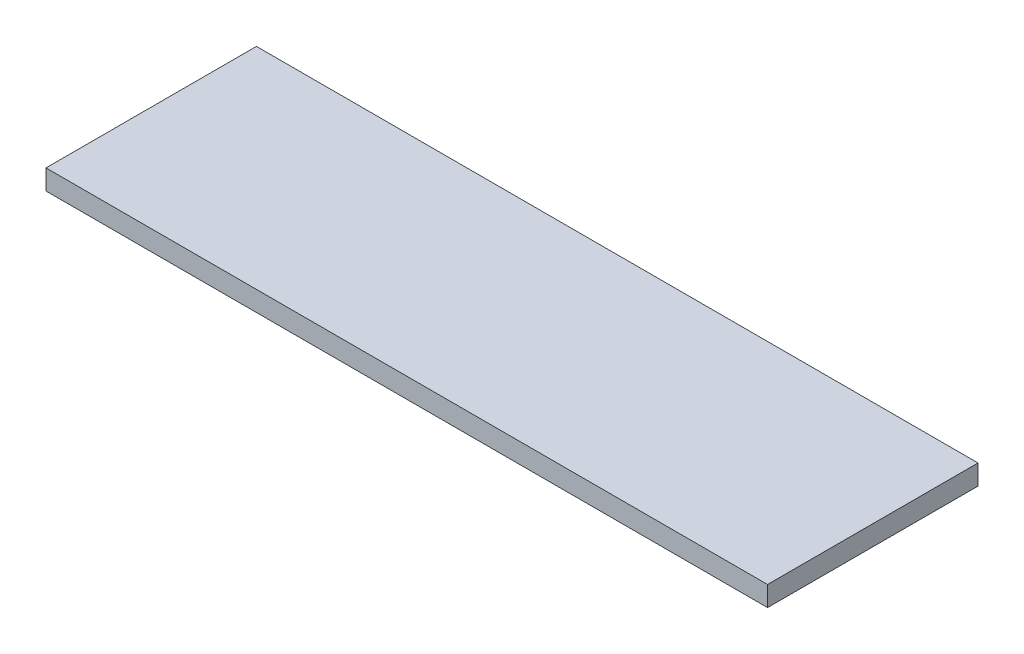
SolidWorks part; units mm, degrees
ref_plane "Front Plane" through (0, 0, 0) normal (0, 0, 1) x (1, 0, 0)
ref_plane "Top Plane" through (0, 0, 0) normal (0, 1, 0) x (1, 0, 0)
ref_plane "Right Plane" through (0, 0, 0) normal (1, 0, 0) x (0, 0, -1)
sketch "Sketch1" plane through (0, 0, 0) normal (0, 1, 0) x (1, 0, 0)
  line L1 (360, -105) -> (-360, -105)
  line L2 (360, -105) -> (360, 105)
  line L3 (360, 105) -> (-360, 105)
  line L4 (-360, -105) -> (-360, 105)
  line L5 (360, -105) -> (-360, 105) construction
  line L6 (360, 105) -> (-360, -105) construction
  point P0 (0, 0)
  dimension "D1" = 210
  dimension "D2" = 720
extrude "Boss-Extrude1" add sketch "Sketch1" along normal blind 20
